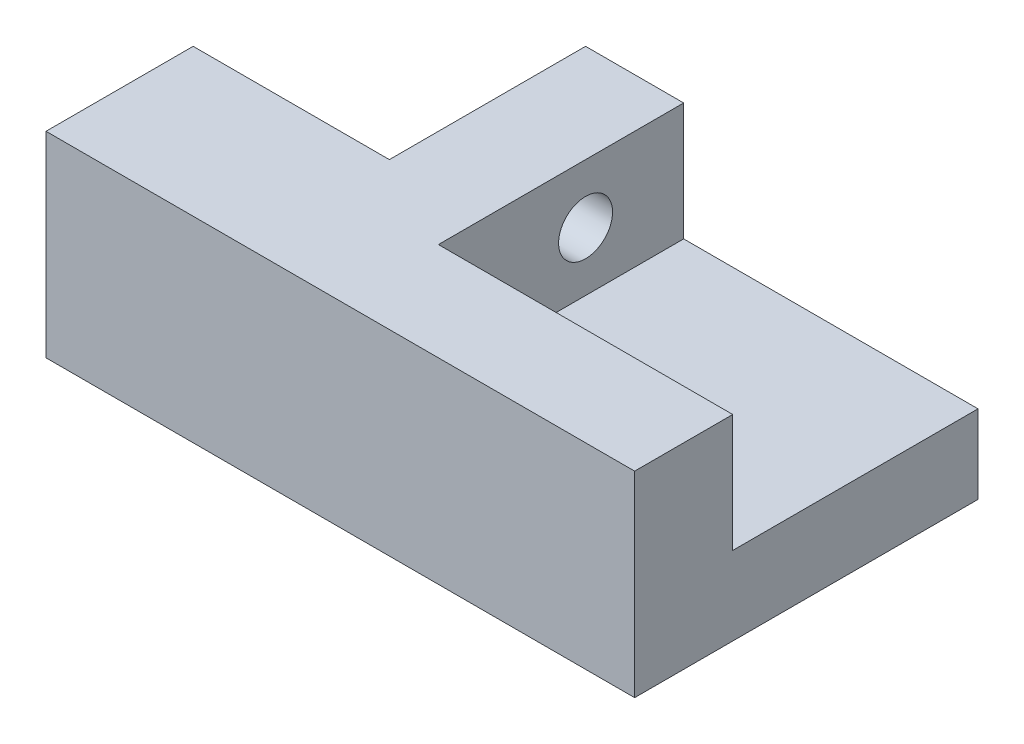
SolidWorks part; units mm, degrees
ref_plane "Front Plane" through (0, 0, 0) normal (0, 0, 1) x (1, 0, 0)
ref_plane "Top Plane" through (0, 0, 0) normal (0, 1, 0) x (1, 0, 0)
ref_plane "Right Plane" through (0, 0, 0) normal (1, 0, 0) x (0, 0, -1)
sketch "Sketch1" plane through (0, 0, 0) normal (0, 1, 0) x (1, 0, 0)
  line L1 (0, 0) -> (60, 0)
  line L2 (0, 0) -> (0, 15)
  line L3 (20, 35) -> (60, 35)
  line L4 (60, 0) -> (60, 35)
  line L7 (0, 15) -> (20, 15)
  line L8 (20, 35) -> (20, 15)
  dimension "D1" = 15
  dimension "D2" = 60
extrude "Boss-Extrude1" add sketch "Sketch1" along normal blind 20
sketch "Sketch2" plane through (0, 20, 0) normal (0, 1, 0) x (1, 0, 0)
  line L0 (20, 35) -> (20, 15) construction
  line L1 (60, 35) -> (30, 35)
  line L2 (60, 35) -> (60, 10)
  line L3 (60, 10) -> (30, 10)
  line L4 (30, 35) -> (30, 10)
  dimension "D1" = 25
  dimension "D2" = 10
extrude "Cut-Extrude1" cut sketch "Sketch2" against normal blind 12
sketch "Sketch3" plane through (0, 8, 0) normal (0, 1, 0) x (1, 0, 0)
  line L0 (30, 35) -> (30, 10) construction
  circle A0 centre (46.1, 12.5258) radius 11.1
  dimension "D1" = 22.2
  dimension "D2" = 5
sketch "Sketch5" plane through (30, 0, 0) normal (1, 0, 0) x (0, 0, -1)
  line L0 (35, 20) -> (10, 20) construction
  line L2 (15, 20) -> (15, 0) construction
  circle A0 centre (25, 14) radius 2.75
  point P4 (22.5, 20)
  dimension "D1" = 5.5
  dimension "D2" = 6
  dimension "D3" = 10
extrude "Cut-Extrude4" cut sketch "Sketch5" against normal through all
sketch "Sketch6" plane through (0, 0, 0) normal (0, -1, 0) x (1, 0, 0)
  circle A0 centre (46.1, -12.5258) radius 6.7
  dimension "D1" = 13.4
extrude "Cut-Extrude5" cut sketch "Sketch6" against normal blind 5
sketch "Sketch7" plane through (0, 5, 0) normal (0, -1, 0) x (1, 0, 0)
  circle A0 centre (46.1, -12.5258) radius 2.5
  dimension "D1" = 5
extrude "Cut-Extrude6" cut sketch "Sketch7" against normal through all
